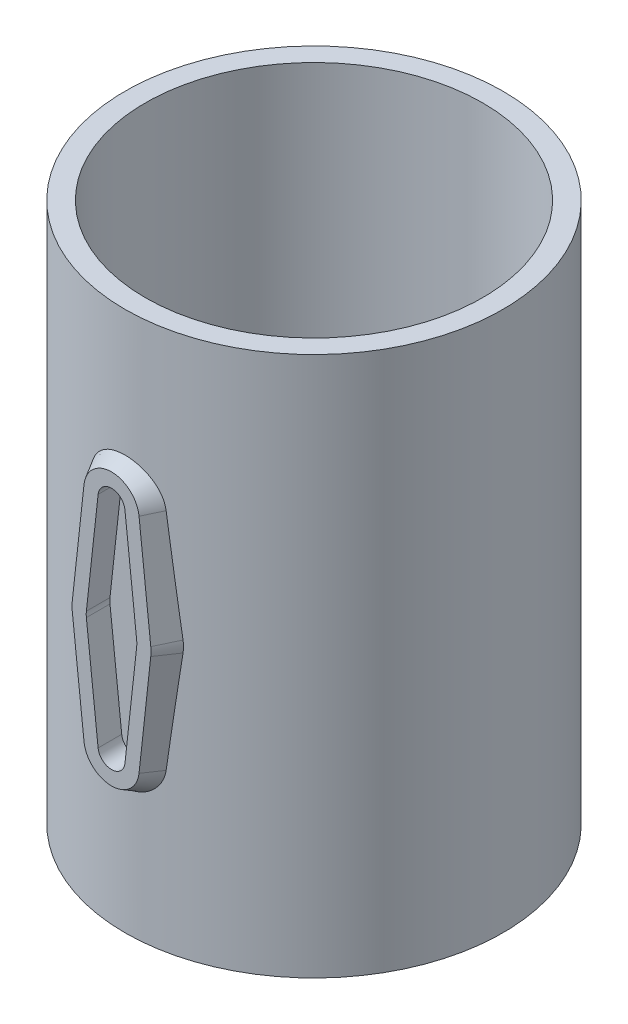
SolidWorks part; units mm, degrees
ref_plane "Ebene vorne" through (0, 0, 0) normal (0, 0, 1) x (1, 0, 0)
ref_plane "Ebene oben" through (0, 0, 0) normal (0, 1, 0) x (1, 0, 0)
ref_plane "Ebene rechts" through (0, 0, 0) normal (1, 0, 0) x (0, 0, -1)
sketch "Sketch1" plane through (0, 0, 0) normal (0, 1, 0) x (1, 0, 0)
  circle A0 centre (0, 0) radius 25
  circle A1 centre (0, 0) radius 28
  dimension "D1" = 50
  dimension "D2" = 56
extrude "Boss-Extrude1" add sketch "Sketch1" along normal blind 80
ref_plane "Plane1" through (0, 0, 26.5) normal (0, 0, 1) x (1, 0, 0)
sketch "Sketch6" plane through (0, 0, 26.5) normal (0, 0, 1) x (1, 0, 0)
  line L0 (0, 80) -> (0, 0) construction
  line L1 (25, 80) -> (-25, 80) construction
  line L2 (-28, 0) -> (28, 0) construction
  line L3 (-28, 40) -> (28, 40) construction
  line L4 (-28, 80) -> (-28, 0) construction
  line L5 (28, 0) -> (28, 80) construction
  line L6 (-3.7276, 40.4089) -> (-1.9881, 56.2681)
  line L7 (3.7276, 40.4089) -> (1.9881, 56.2681)
  line L8 (3.7276, 39.5911) -> (1.9881, 23.7319)
  line L9 (-3.7276, 39.5911) -> (-1.9881, 23.7319)
  line L10 (-3.827, 40.4198) -> (-2.0875, 56.279)
  line L11 (3.827, 40.4198) -> (2.0875, 56.279)
  line L12 (3.827, 39.5802) -> (2.0875, 23.721)
  line L13 (-3.827, 39.5802) -> (-2.0875, 23.721)
  arc A0 (-3.7276, 40.4089) -> (-3.7276, 39.5911) centre (0, 40) ccw
  arc A1 (1.9881, 56.2681) -> (-1.9881, 56.2681) centre (0, 56.05) ccw
  arc A2 (1.9881, 23.7319) -> (-1.9881, 23.7319) centre (0, 23.95) cw
  arc A3 (3.7276, 39.5911) -> (3.7276, 40.4089) centre (0, 40) ccw
  arc A4 (2.0875, 56.279) -> (-2.0875, 56.279) centre (0, 56.05) ccw
  arc A5 (3.827, 39.5802) -> (3.827, 40.4198) centre (0, 40) ccw
  arc A6 (2.0875, 23.721) -> (-2.0875, 23.721) centre (0, 23.95) cw
  arc A7 (-3.827, 40.4198) -> (-3.827, 39.5802) centre (0, 40) ccw
  point P35 (0, 0)
  dimension "D1" = 7.5
  dimension "D2" = 4
  dimension "D3" = 16.05
  dimension "D4" = 0.1
extrude "Cut-Extrude3" cut sketch "Sketch6" along normal through all contours A3 L7 A1 L6 A0 L9 A2 L8
sketch "Sketch7" plane through (0, 0, 26.5) normal (0, 0, 1) x (1, 0, 0)
  line L4 (1.9881, 23.7319) -> (3.7276, 39.5911)
  line L5 (-3.7276, 39.5911) -> (-1.9881, 23.7319)
  line L6 (-1.9881, 56.2681) -> (-3.7276, 40.4089)
  line L7 (3.7276, 40.4089) -> (1.9881, 56.2681)
  line L8 (1.9881, 23.7319) -> (3.7276, 39.5911)
  line L9 (-3.7276, 39.5911) -> (-1.9881, 23.7319)
  line L10 (-1.9881, 56.2681) -> (-3.7276, 40.4089)
  line L11 (3.7276, 40.4089) -> (1.9881, 56.2681)
  arc A4 (-1.9881, 23.7319) -> (1.9881, 23.7319) centre (0, 23.95) ccw
  arc A5 (-3.7276, 40.4089) -> (-3.7276, 39.5911) centre (0, 40) ccw
  arc A6 (1.9881, 56.2681) -> (-1.9881, 56.2681) centre (0, 56.05) ccw
  arc A7 (3.7276, 39.5911) -> (3.7276, 40.4089) centre (0, 40) ccw
  arc A8 (-1.9881, 23.7319) -> (1.9881, 23.7319) centre (0, 23.95) ccw
  arc A9 (-3.7276, 40.4089) -> (-3.7276, 39.5911) centre (0, 40) ccw
  arc A10 (1.9881, 56.2681) -> (-1.9881, 56.2681) centre (0, 56.05) ccw
  arc A11 (3.7276, 39.5911) -> (3.7276, 40.4089) centre (0, 40) ccw
  dimension "D1" = 0
extrude "Extrude-Thin2" add sketch "Sketch7" along normal blind 3.5 thin
sketch "Sketch9" plane through (0, 0, 30) normal (0, 0, 1) x (1, 0, 0)
  line L4 (3.9762, 23.5139) -> (5.7157, 39.3731)
  line L5 (-5.7157, 39.3731) -> (-3.9762, 23.5139)
  line L6 (-3.9762, 56.4861) -> (-5.7157, 40.6269)
  line L7 (5.7157, 40.6269) -> (3.9762, 56.4861)
  line L8 (3.9762, 23.5139) -> (5.7157, 39.3731)
  line L9 (-5.7157, 39.3731) -> (-3.9762, 23.5139)
  line L10 (-3.9762, 56.4861) -> (-5.7157, 40.6269)
  line L11 (5.7157, 40.6269) -> (3.9762, 56.4861)
  arc A4 (5.7157, 39.3731) -> (5.7157, 40.6269) centre (0, 40) ccw
  arc A5 (-3.9762, 23.5139) -> (3.9762, 23.5139) centre (0, 23.95) ccw
  arc A6 (-5.7157, 40.6269) -> (-5.7157, 39.3731) centre (0, 40) ccw
  arc A7 (3.9762, 56.4861) -> (-3.9762, 56.4861) centre (0, 56.05) ccw
  arc A8 (5.7157, 39.3731) -> (5.7157, 40.6269) centre (0, 40) ccw
  arc A9 (-3.9762, 23.5139) -> (3.9762, 23.5139) centre (0, 23.95) ccw
  arc A10 (-5.7157, 40.6269) -> (-5.7157, 39.3731) centre (0, 40) ccw
  arc A11 (3.9762, 56.4861) -> (-3.9762, 56.4861) centre (0, 56.05) ccw
  dimension "D1" = 0
extrude "Extrude-Thin3" add sketch "Sketch9" against normal up to next draft 30 thin
ref_plane "Plane2" through (0, 0, -26.5) normal (0, 0, 1) x (1, 0, 0)
sketch "Sketch10" plane through (0, 0, -26.5) normal (0, 0, 1) x (1, 0, 0)
  line L0 (28, 40) -> (-28, 40) construction
  line L1 (28, 0) -> (28, 80) construction
  line L2 (-28, 80) -> (-28, 0) construction
  line L3 (0, 80) -> (0, 0) construction
  line L4 (25, 80) -> (-25, 80) construction
  line L6 (-3.5, 36.5) -> (3.5, 36.5)
  line L7 (-3.5, 36.5) -> (-3.5, 43.5)
  line L8 (-3.5, 43.5) -> (3.5, 43.5)
  line L9 (3.5, 36.5) -> (3.5, 43.5)
  line L10 (-3.5, 36.5) -> (3.5, 43.5) construction
  line L11 (-3.5, 43.5) -> (3.5, 36.5) construction
  point P11 (0, 40)
  dimension "D1" = 7
  dimension "D2" = 7
extrude "Cut-Extrude4" cut sketch "Sketch10" against normal blind 3
